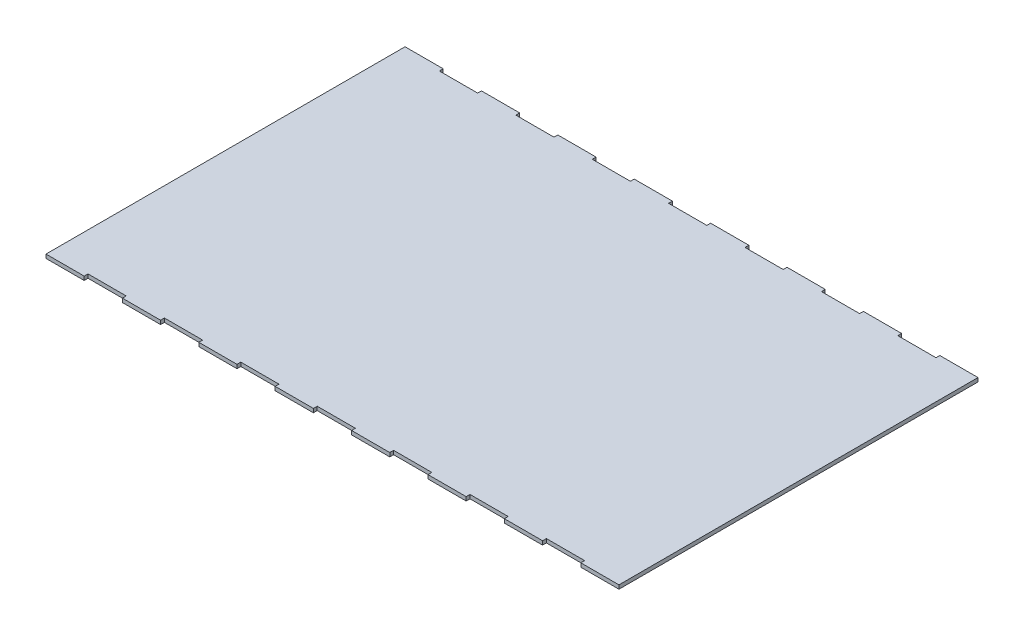
SolidWorks part; units mm, degrees
ref_plane "Front Plane" through (0, 0, 0) normal (0, 0, 1) x (1, 0, 0)
ref_plane "Top Plane" through (0, 0, 0) normal (0, 1, 0) x (1, 0, 0)
ref_plane "Right Plane" through (0, 0, 0) normal (1, 0, 0) x (0, 0, -1)
sketch "Sketch1" plane through (0, 0, 0) normal (0, 1, 0) x (1, 0, 0)
  line L1 (-224.2814, 65.7352) -> (75.7186, 65.7352)
  line L2 (-224.2814, 65.7352) -> (-224.2814, -122.2648)
  line L3 (-224.2814, -122.2648) -> (75.7186, -122.2648)
  line L4 (75.7186, 65.7352) -> (75.7186, -122.2648)
  dimension "D1" = 300
  dimension "D2" = 188
extrude "Boss-Extrude1" add sketch "Sketch1" along normal blind 2
sketch "Sketch2" plane through (0, 2, 0) normal (0, 1, 0) x (1, 0, 0)
  line L7 (-204.2814, -122.2648) -> (-184.2814, -122.2648)
  line L8 (-204.2814, -122.2648) -> (-204.2814, -120.2648)
  line L9 (-204.2814, -120.2648) -> (-184.2814, -120.2648)
  line L10 (-184.2814, -122.2648) -> (-184.2814, -120.2648)
  line L11 (-224.2814, -122.2648) -> (75.7186, -122.2648) construction
  line L12 (-224.2814, 65.7352) -> (-224.2814, -122.2648) construction
  dimension "D1" = 20
  dimension "D2" = 2
  dimension "D3" = 0
  dimension "D4" = 20
extrude "Cut-Extrude1" cut sketch "Sketch2" against normal blind 4
pattern_linear "LPattern1" count 8 spacing 40 along (1, 0, 0) of "Cut-Extrude1"
sketch "Sketch3" plane through (0, 2, 0) normal (0, 1, 0) x (1, 0, 0)
  line L0 (-98.9758, -28.2648) -> (53.2653, -28.2648)
  line L3 (-144.2814, -122.2648) -> (-124.2814, -122.2648) construction
  line L4 (75.7186, 65.7352) -> (-224.2814, 65.7352) construction
  dimension "D1" = 152.241
  dimension "D2" = 94
  dimension "D3" = 94
ref_plane "Plane1" through (0, 0, 28.2648) normal (0, 0, 1) x (1, 0, 0)
mirror "Mirror1" about plane through (0, 0, 28.2648) normal (0, 0, 1) of "LPattern1", "Cut-Extrude1"
